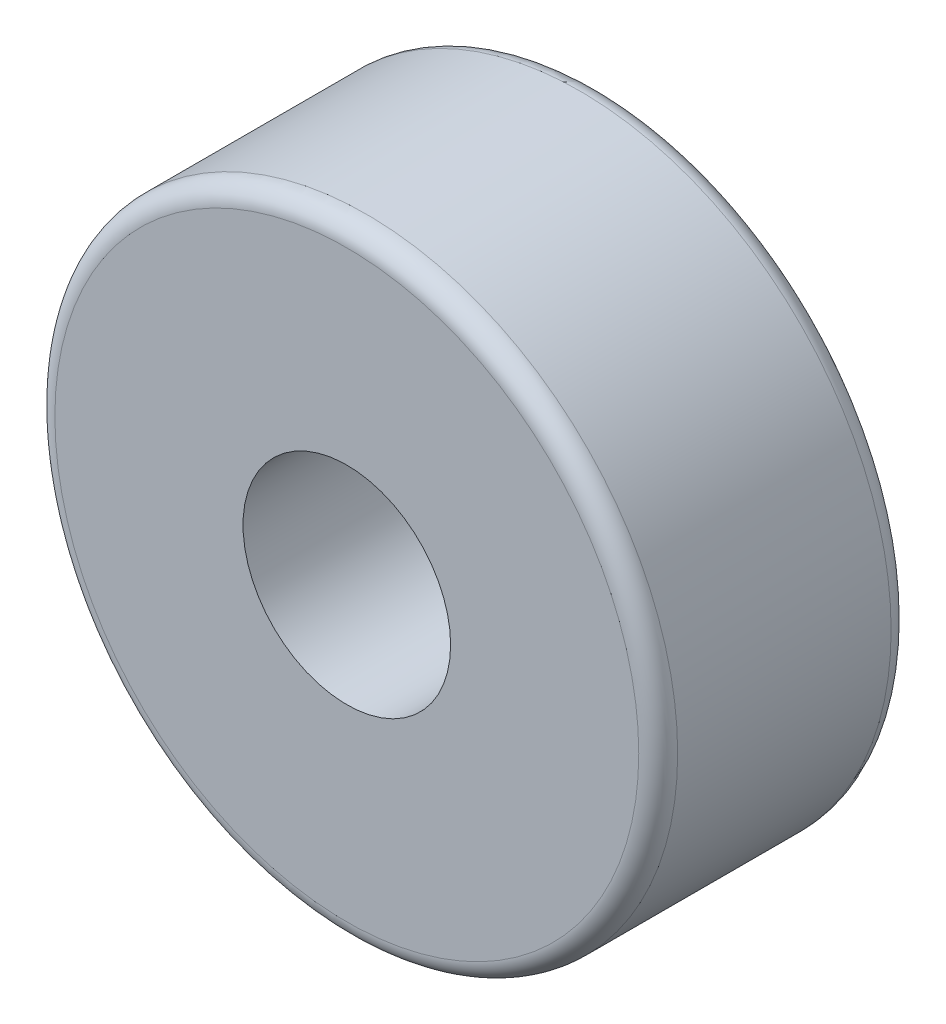
SolidWorks part; units mm, degrees
ref_plane "Front Plane" through (0, 0, 0) normal (0, 0, 1) x (1, 0, 0)
ref_plane "Top Plane" through (0, 0, 0) normal (0, 1, 0) x (1, 0, 0)
ref_plane "Right Plane" through (0, 0, 0) normal (1, 0, 0) x (0, 0, -1)
sketch "Sketch1" plane through (0, 0, 0) normal (0, 0, 1) x (1, 0, 0)
  line L0 (-32.5405, 0) -> (33.3106, 0) construction
  circle A0 centre (0, 0) radius 12.7
  dimension "D1" = 25.4
extrude "Extrude-Thin1" add sketch "Sketch1" along normal blind 30.8769 thin
fillet "Fillet1" radius 2.38 2 edges at (38.1, 0, 0) (38.1, 0, 30.8769)
